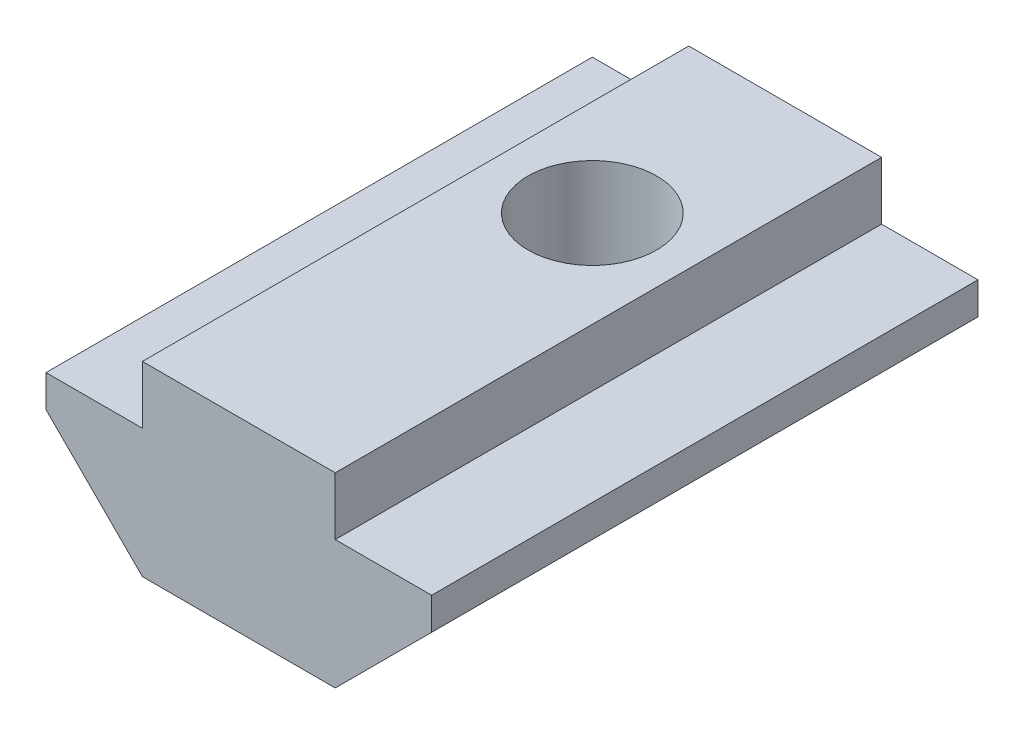
SolidWorks part; units mm, degrees
ref_plane "Piano frontale" through (0, 0, 0) normal (0, 0, 1) x (1, 0, 0)
ref_plane "Piano superiore" through (0, 0, 0) normal (0, 1, 0) x (1, 0, 0)
ref_plane "Piano destro" through (0, 0, 0) normal (1, 0, 0) x (0, 0, -1)
sketch "Schizzo1" plane through (0, 0, 0) normal (0, 0, 1) x (1, 0, 0)
  line L0 (3, 0) -> (-3, 0)
  line L1 (-3, 0) -> (-6, 3)
  line L2 (-6, 3) -> (-6, 4)
  line L3 (-6, 4) -> (-3, 4)
  line L4 (-3, 4) -> (-3, 5.8)
  line L5 (-3, 5.8) -> (3, 5.8)
  line L6 (3, 4) -> (3, 5.8)
  line L7 (6, 4) -> (3, 4)
  line L8 (6, 3) -> (6, 4)
  line L9 (3, 0) -> (6, 3)
  point P0 (0, 0)
  dimension "D1" = 5.8
  dimension "D2" = 4
  dimension "D3" = 1
  dimension "D4" = 45
  dimension "D5" = 6
  dimension "D6" = 12
  dimension "D7" = 45
  dimension "D8" = 6
  dimension "D9" = 4
  dimension "D10" = 3
extrude "Estrusione-Estrusione1" add sketch "Schizzo1" along normal blind 17
sketch "Schizzo2" plane through (0, 5.8, 0) normal (0, 1, 0) x (1, 0, 0)
  circle A0 centre (0, -6) radius 2
  dimension "D1" = 4
  dimension "D2" = 6
extrude "Taglio-Estrusione1" cut sketch "Schizzo2" against normal through all
cosmetic thread "Filettatura cosmetica1" parameters "D2"=5
sketch "Schizzo4" plane through (0, 0, 0) normal (1, 0, 0) x (0, 0, -1)
  line L0 (-12, 0) -> (-12, -2.8784) construction
  line L1 (-12, -1.5) -> (-12, 0)
  line L2 (-12, 0) -> (-13.5, 0)
  line L3 (-17, 0) -> (0, 0) construction
  line L4 (-17, 0) -> (-17, 3) construction
  arc A0 (-12, -1.5) -> (-13.5, 0) centre (-12, 0) cw
  dimension "D1" = 1.5
  dimension "D2" = 5
revolve "Rivoluzione2" add sketch "Schizzo4" angle 360 about L0
